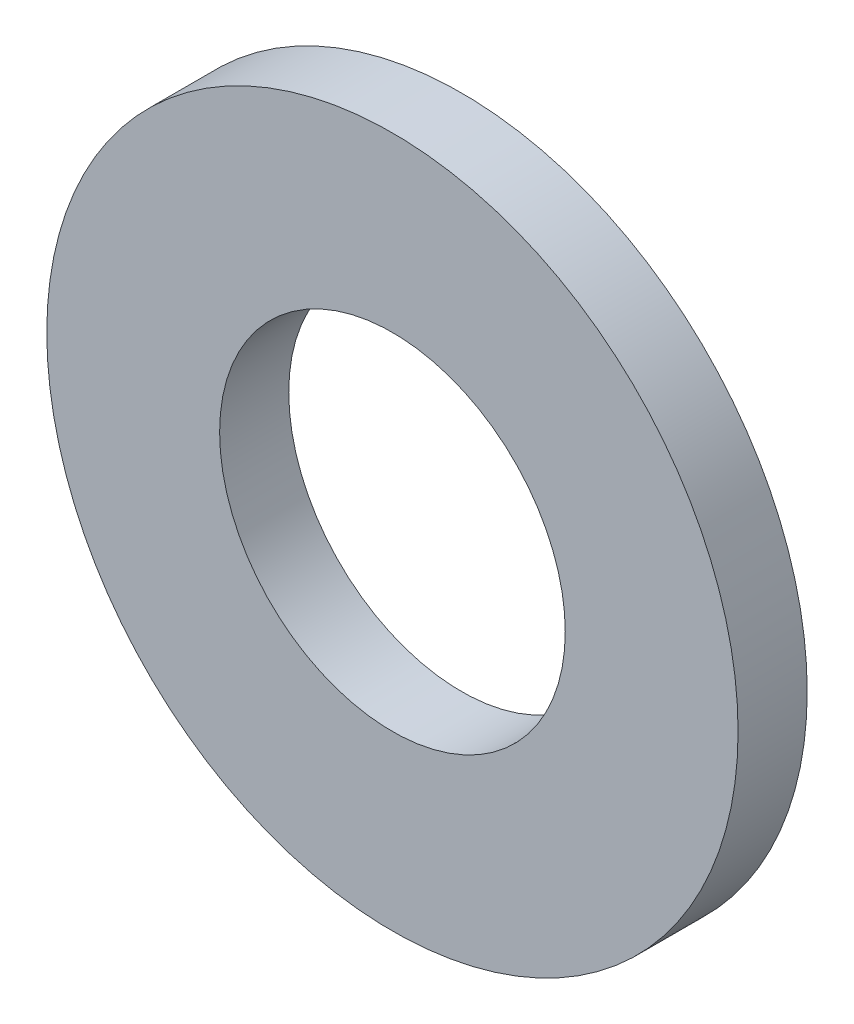
SolidWorks part; units mm, degrees
ref_plane "Front Plane" through (0, 0, 0) normal (0, 0, 1) x (1, 0, 0)
ref_plane "Top Plane" through (0, 0, 0) normal (0, 1, 0) x (1, 0, 0)
ref_plane "Right Plane" through (0, 0, 0) normal (1, 0, 0) x (0, 0, -1)
sketch "Sketch1" plane through (0, 0, 0) normal (0, 0, 1) x (1, 0, 0)
  circle A0 centre (0, 0) radius 2
  circle A1 centre (0, 0) radius 1
extrude "Boss-Extrude1" add sketch "Sketch1" along normal blind 0.4
